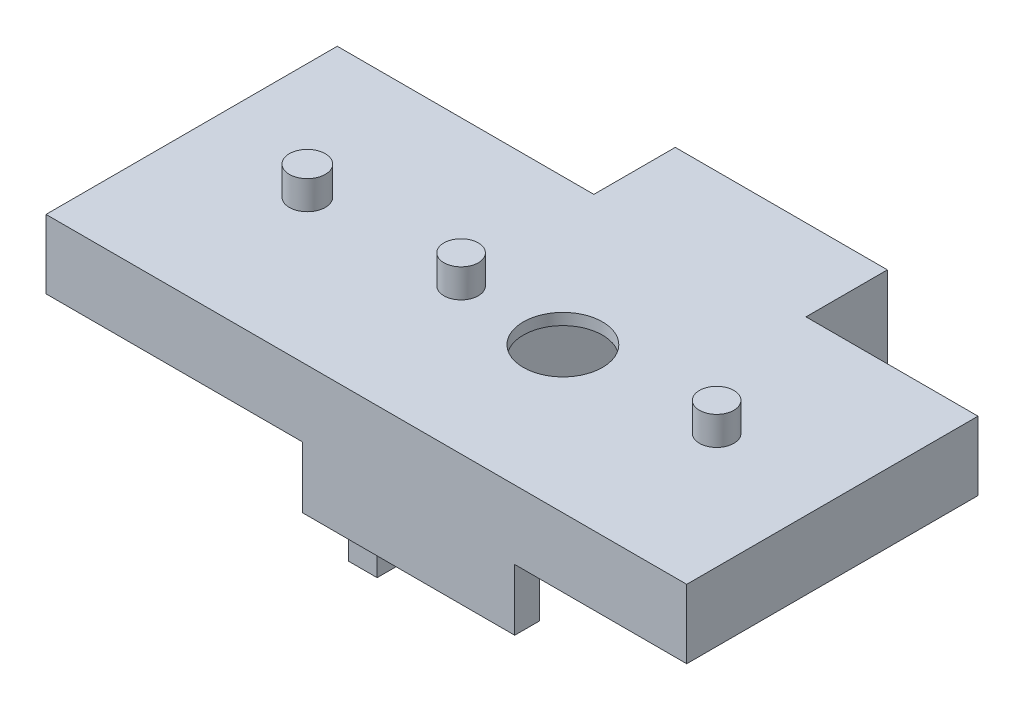
SolidWorks part; units mm, degrees
ref_plane "Front Plane" through (0, 0, 0) normal (0, 0, 1) x (1, 0, 0)
ref_plane "Top Plane" through (0, 0, 0) normal (0, 1, 0) x (1, 0, 0)
ref_plane "Right Plane" through (0, 0, 0) normal (1, 0, 0) x (0, 0, -1)
sketch "Sketch3" plane through (0, 0, 0) normal (1, 0, 0) x (0, 0, -1)
  line L1 (-28.5, 17) -> (28.5, 17)
  line L2 (-28.5, 17) -> (-28.5, -17)
  line L3 (-28.5, -17) -> (28.5, -17)
  line L4 (28.5, 17) -> (28.5, -17)
  line L5 (-28.5, 17) -> (28.5, -17) construction
  line L6 (-28.5, -17) -> (28.5, 17) construction
  circle A0 centre (-24.8, -3.1) radius 2.2
  circle A1 centre (-24.8, -13) radius 2.2
  circle A2 centre (24.2, -3.1) radius 2.2
  circle A3 centre (24.2, -13) radius 2.2
  point P0 (0, 0)
  dimension "D3" = 4.4
  dimension "D4" = 4.4
  dimension "D5" = 4.4
  dimension "D6" = 4.4
  dimension "D8" = 3.7
  dimension "D9" = 49
  dimension "D11" = 9.9
  dimension "D12" = 9.9
  dimension "D13" = 20.1
  dimension "D14" = 20.1
  dimension "D1" = 57
  dimension "D2" = 34
  dimension "D7" = 3.7
extrude "Boss-Extrude2" add sketch "Sketch3" along normal blind 5
sketch "Sketch4" plane through (5, 0, 0) normal (1, 0, 0) x (0, 0, -1)
  line L0 (-28.5, 17) -> (12, 17)
  line L3 (12, 15) -> (-20, 15)
  line L4 (-20, 15) -> (-20, 10.5)
  line L5 (-20, 10.5) -> (-28.5, 10.5)
  line L6 (-28.5, 17) -> (-28.5, -17) construction
  line L7 (-28.5, 10.5) -> (-28.5, 17)
  line L8 (12, 17) -> (12, 15)
  dimension "D1" = 2
  dimension "D2" = 6.5
  dimension "D3" = 8.5
  dimension "D4" = 32
extrude "Boss-Extrude3" add sketch "Sketch4" along normal blind 32
sketch "Sketch5" plane through (0, 17, 0) normal (0, 1, 0) x (1, 0, 0)
  line L0 (0, 28.5) -> (0, -28.5) construction
  line L1 (37, -28.5) -> (0, -28.5) construction
  circle A0 centre (20, -11.1) radius 6.9
  dimension "D1" = 13.8
  dimension "D2" = 20
  dimension "D3" = 17.4
extrude "Cut-Extrude1" cut sketch "Sketch5" against normal blind 19
sketch "Sketch6" plane through (0, 0, 28.5) normal (0, 0, 1) x (1, 0, 0)
  line L0 (0, 17) -> (37, 17)
  line L1 (37, 17) -> (37, 10.5)
  line L2 (37, 10.5) -> (5, 10.5)
  line L3 (5, 10.5) -> (5, -5.6961)
  line L4 (5, 10.5) -> (5, -17) construction
  line L5 (5, -5.6961) -> (0, -5.6961)
  line L6 (0, 17) -> (0, -17) construction
  line L7 (0, -5.6961) -> (0, 17)
extrude "Boss-Extrude4" add sketch "Sketch6" along normal blind 8
sketch "Sketch7" plane through (0, 0, 20) normal (0, 0, -1) x (-1, 0, 0)
  line L0 (-37, 15) -> (-5, 15) construction
  line L1 (-37, 10.5) -> (-31, 10.5)
  line L2 (-37, 10.5) -> (-37, 15)
  line L3 (-37, 15) -> (-31, 15)
  line L4 (-31, 10.5) -> (-31, 15)
  dimension "D1" = 6
extrude "Boss-Extrude5" add sketch "Sketch7" along normal blind 39.5
sketch "Sketch8" plane through (5, 0, 0) normal (1, 0, 0) x (0, 0, -1)
  line L0 (-36.5, 10.5) -> (-20, 10.5) construction
  line L1 (-36.5, -5.6961) -> (-32.1714, -5.6961)
  line L2 (-36.5, -5.6961) -> (-36.5, 10.5)
  line L3 (-36.5, 10.5) -> (-32.1714, 10.5)
  line L4 (-32.1714, -5.6961) -> (-32.1714, 2.0895)
  line L5 (-36.5, -5.6961) -> (-36.5, 10.5) construction
  line L6 (-36.5, -5.6961) -> (-28.5, -5.6961) construction
  line L7 (-32.1714, 10.5) -> (-29.6551, 10.5)
  line L9 (-32.1714, 2.0895) -> (-29.6551, 2.0895)
  line L10 (-29.6551, 10.5) -> (-29.6551, 2.0895)
  point P7 (-36.5, -5.6961)
  point P8 (-32.1714, -5.6961)
extrude "Boss-Extrude6" add sketch "Sketch8" along normal up to vertex (32 mm away)
sketch "Sketch9" plane through (5, 0, 0) normal (1, 0, 0) x (0, 0, -1)
  line L0 (12, 17) -> (28.5, 17)
  line L1 (28.5, 17) -> (28.5, 12)
  line L2 (28.5, -17) -> (28.5, 17) construction
  line L3 (28.5, 12) -> (19.5, 12)
  line L4 (19.5, 12) -> (19.5, 15)
  line L5 (19.5, 15) -> (12, 15)
  line L6 (12, 15) -> (12, 17)
  point P8 (12, 15)
  dimension "D1" = 9
  dimension "D2" = 5
extrude "Boss-Extrude7" add sketch "Sketch9" along normal up to vertex (32 mm away)
sketch "Sketch11" plane through (0, 0, 29.6551) normal (0, 0, -1) x (-1, 0, 0)
  line L0 (-37, 10.5) -> (-5, 10.5) construction
  line L1 (-37, 2.0895) -> (-31, 2.0895)
  line L2 (-37, 2.0895) -> (-37, 10.5)
  line L3 (-37, 10.5) -> (-31, 10.5)
  line L4 (-31, 2.0895) -> (-31, 10.5)
  dimension "D1" = 6
extrude "Boss-Extrude8" add sketch "Sketch11" along normal up to vertex (58.1551 mm away)
sketch "Sketch12" plane through (0, 0, -19.5) normal (0, 0, -1) x (-1, 0, 0)
  line L1 (-37, 10.5) -> (-31, 10.5)
  line L2 (-37, 10.5) -> (-37, 12)
  line L3 (-37, 12) -> (-31, 12)
  line L4 (-31, 10.5) -> (-31, 12)
extrude "Boss-Extrude9" add sketch "Sketch12" along normal up to vertex (9 mm away)
sketch "Sketch13" plane through (37, 0, 0) normal (1, 0, 0) x (0, 0, -1)
  line L6 (-36.5, 17) -> (14.3, 17)
  line L7 (-36.5, 17) -> (-36.5, 5)
  line L8 (-36.5, 5) -> (14.3, 5)
  line L9 (14.3, 17) -> (14.3, 5)
  dimension "D1" = 50.8
  dimension "D2" = 12
extrude "Boss-Extrude10" add sketch "Sketch13" along normal blind 30
sketch "Sketch14" plane through (0, 0, 0) normal (-1, 0, 0) x (0, 0, 1)
  line L1 (36.5, 17) -> (-14.3, 17)
  line L2 (36.5, 17) -> (36.5, 5)
  line L3 (36.5, 5) -> (-14.3, 5)
  line L4 (-14.3, 17) -> (-14.3, 5)
  dimension "D1" = 50.8
  dimension "D2" = 12
extrude "Boss-Extrude11" add sketch "Sketch14" along normal blind 44.75
sketch "Sketch15" plane through (0, 17, 0) normal (0, 1, 0) x (1, 0, 0)
  circle A0 centre (2.25, -11.1) radius 3
  circle A1 centre (20, -11.1) radius 6.9 construction
  circle A2 centre (46.82, -11.1) radius 3
  circle A3 centre (-24.57, -11.1) radius 3.1291
  dimension "D1" = 17.75
  dimension "D2" = 6
  dimension "D3" = 26.82
  dimension "D4" = 6
  dimension "D5" = 26.82
extrude "Boss-Extrude12" add sketch "Sketch15" along normal blind 5
